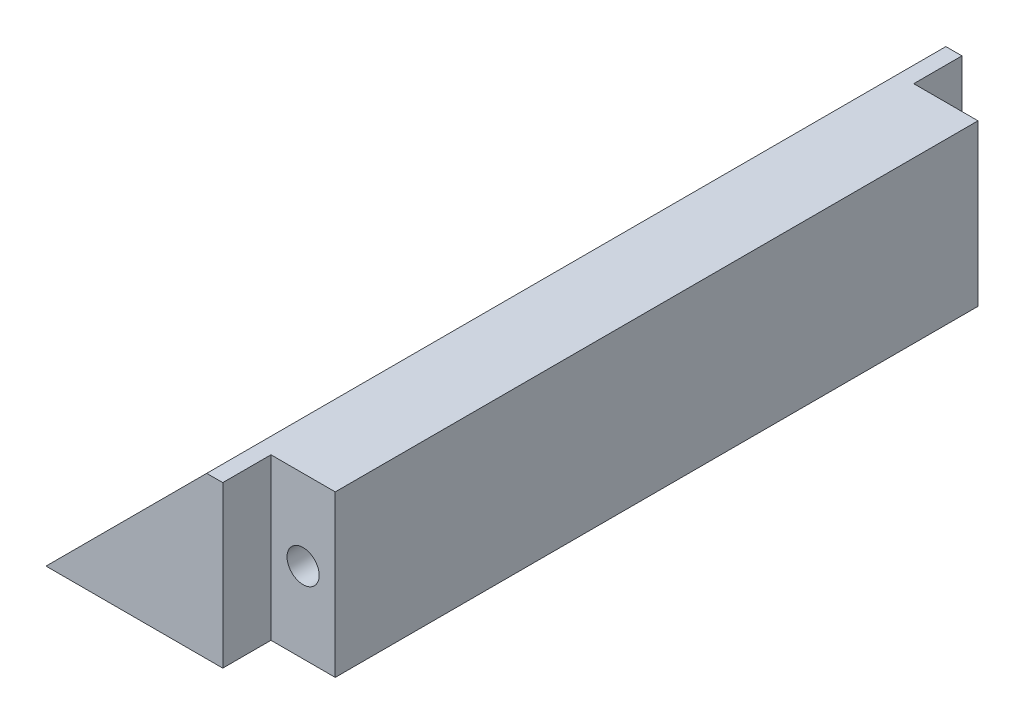
SolidWorks part; units mm, degrees
material "Malleable Cast Iron"
ref_plane "Front Plane" through (0, 0, 0) normal (0, 0, 1) x (1, 0, 0)
ref_plane "Top Plane" through (0, 0, 0) normal (0, 1, 0) x (1, 0, 0)
ref_plane "Right Plane" through (0, 0, 0) normal (1, 0, 0) x (0, 0, -1)
sketch "Sketch1" plane through (0, 0, 0) normal (0, 0, 1) x (1, 0, 0)
  line L0 (-37.1001, 13.3467) -> (-47.1001, 3.3467)
  line L1 (-32.1001, 13.3467) -> (-37.1001, 13.3467)
  line L2 (-32.1001, 3.3467) -> (-32.1001, 13.3467)
  line L3 (-32.1001, 3.3467) -> (-47.1001, 3.3467)
extrude "Boss-Extrude1" add sketch "Sketch1" along normal blind 52
sketch "Sketch4" plane through (0, 0, 52) normal (0, 0, 1) x (1, 0, 0)
  line L2 (-32.1001, 13.3467) -> (-36.1001, 13.3467)
  line L3 (-32.1001, 13.3467) -> (-32.1001, 3.3467)
  line L4 (-32.1001, 3.3467) -> (-36.1001, 3.3467)
  line L5 (-36.1001, 13.3467) -> (-36.1001, 3.3467)
  dimension "D1" = 4
  dimension "D2" = 10
extrude "Cut-Extrude1" cut sketch "Sketch4" against normal blind 6
sketch "Sketch5" plane through (0, 0, 0) normal (0, 0, -1) x (-1, 0, 0)
  line L2 (32.1001, 13.3467) -> (36.1001, 13.3467)
  line L3 (32.1001, 13.3467) -> (32.1001, 3.3467)
  line L4 (32.1001, 3.3467) -> (36.1001, 3.3467)
  line L5 (36.1001, 13.3467) -> (36.1001, 3.3467)
  dimension "D1" = 4
  dimension "D2" = 10
extrude "Cut-Extrude2" cut sketch "Sketch5" against normal blind 6
sketch "Sketch6" plane through (0, 0, 52) normal (0, 0, 1) x (1, 0, 0)
  line L0 (-47.1001, 3.3467) -> (-37.1001, 13.3467)
  line L1 (-37.1001, 13.3467) -> (-36.1001, 13.3467)
  line L2 (-36.1001, 13.3467) -> (-36.1001, 3.3467)
  line L3 (-36.1001, 3.3467) -> (-47.1001, 3.3467)
extrude "Cut-Extrude3" cut sketch "Sketch6" against normal blind 3
sketch "Sketch7" plane through (0, 0, 0) normal (0, 0, -1) x (-1, 0, 0)
  line L0 (47.1001, 3.3467) -> (37.1001, 13.3467)
  line L1 (37.1001, 13.3467) -> (36.1001, 13.3467)
  line L2 (36.1001, 13.3467) -> (36.1001, 3.3467)
  line L3 (36.1001, 3.3467) -> (47.1001, 3.3467)
extrude "Cut-Extrude4" cut sketch "Sketch7" against normal blind 3
sketch "Sketch8" plane through (0, 0, 6) normal (0, 0, -1) x (-1, 0, 0)
  circle A0 centre (34.1001, 8.3467) radius 1
extrude "Cut-Extrude5" cut sketch "Sketch8" against normal blind 10
sketch "Sketch9" plane through (0, 0, 46) normal (0, 0, 1) x (1, 0, 0)
  circle A0 centre (-34.1001, 8.3467) radius 1
extrude "Cut-Extrude6" cut sketch "Sketch9" against normal blind 10
